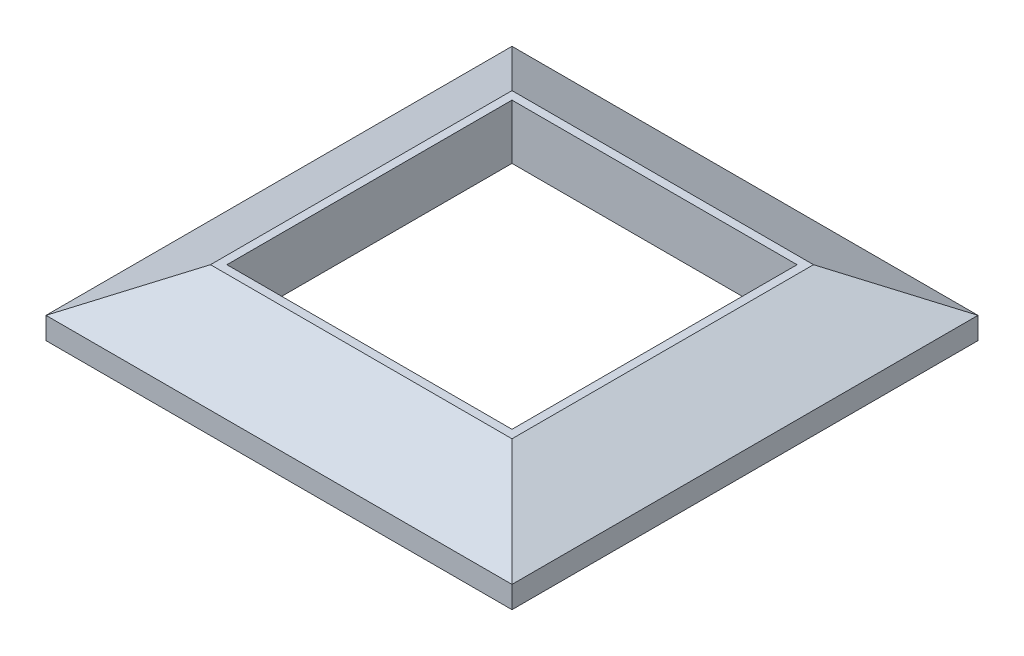
SolidWorks part; units mm, degrees
ref_plane "Спереди" through (0, 0, 0) normal (0, 0, 1) x (1, 0, 0)
ref_plane "Сверху" through (0, 0, 0) normal (0, 1, 0) x (1, 0, 0)
ref_plane "Справа" through (0, 0, 0) normal (1, 0, 0) x (0, 0, -1)
sketch "Эскиз1" plane through (0, 0, 0) normal (0, 0, 1) x (1, 0, 0)
  line L0 (0, 0) -> (-85, 0)
  line L1 (-85, 0) -> (-85, 4)
  line L2 (-85, 4) -> (-70, 12)
  line L3 (-70, 12) -> (-15, 12)
  line L4 (0, 0) -> (0, 4)
  line L5 (0, 4) -> (-15, 12)
  point P2 (0, 0)
  point P7 (-42.5, 0)
  point P8 (-42.5, 12)
  point P9 (0, 0)
  point P10 (0, 0)
  point P11 (0, 0)
extrude "Бобышка-Вытянуть1" add sketch "Эскиз1" along normal mid plane 85
sketch "Эскиз2" plane through (0, 0, 0) normal (1, 0, 0) x (0, 0, -1)
  line L4 (-42.5, 4) -> (-42.5, 0)
  line L6 (-42.5, 0) -> (42.5, 0)
  line L9 (-42.5, 4) -> (-27.5, 12)
  line L10 (-42.5, 12) -> (42.5, 12) construction
  line L12 (-27.5, 12) -> (27.5, 12)
  line L13 (0, 21.6743) -> (0, -6.8728) construction
  line L14 (42.5, 4) -> (27.5, 12)
  line L15 (42.5, 4) -> (42.5, 0)
  point P2 (0, 0)
  point P13 (0, 12)
  point P15 (0, 0)
extrude "Вырез-Вытянуть1" cut sketch "Эскиз2" against normal through all flip side to cut
sketch "Эскиз3" plane through (0, 0, 0) normal (0, -1, 0) x (1, 0, 0)
  line L1 (-68.5, 26) -> (-16.5, 26)
  line L2 (-68.5, 26) -> (-68.5, -26)
  line L3 (-68.5, -26) -> (-16.5, -26)
  line L4 (-16.5, 26) -> (-16.5, -26)
  line L5 (-68.5, 26) -> (-16.5, -26) construction
  line L6 (-68.5, -26) -> (-16.5, 26) construction
  point P0 (-42.5, 0)
  point P5 (0, 0)
  point P6 (0, 0)
extrude "Вырез-Вытянуть2" cut sketch "Эскиз3" against normal through all
sketch "Эскиз4" plane through (0, 0, 0) normal (0, -1, 0) x (1, 0, 0)
  line L17 (-83.5, 41) -> (-1.5, 41)
  line L18 (-83.5, 41) -> (-83.5, -41)
  line L19 (-83.5, -41) -> (-1.5, -41)
  line L20 (-1.5, 41) -> (-1.5, -41)
  point P4 (0, 0)
  point P5 (0, 0)
  point P6 (0, 0)
  point P7 (0, 0)
  point P8 (0, 0)
extrude "Вырез-Вытянуть3" cut sketch "Эскиз4" against normal blind 2
